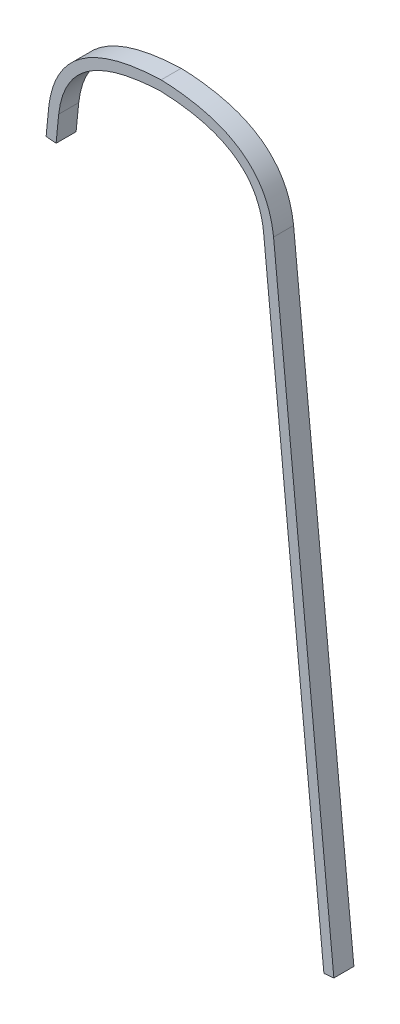
SolidWorks part; units mm, degrees
ref_plane "Front Plane" through (0, 0, 0) normal (0, 0, 1) x (1, 0, 0)
ref_plane "Top Plane" through (0, 0, 0) normal (0, 1, 0) x (1, 0, 0)
ref_plane "Right Plane" through (0, 0, 0) normal (1, 0, 0) x (0, 0, -1)
sketch "Sketch1" plane through (0, 0, 0) normal (0, 0, 1) x (1, 0, 0)
  line L0 (154.7163, 154.5179) -> (97.404, 735.8286)
  line L1 (-99.8892, 710.6217) -> (-97.404, 735.8286)
  line L2 (-109.3682, 711.5562) -> (-99.8892, 710.6217)
  line L3 (154.7163, 154.5179) -> (164.1954, 155.4524)
  line L4 (-166.6875, 130.175) -> (-106.8761, 736.8337) construction
  line L5 (-156.6942, 134.4562) -> (-97.404, 735.8286) construction
  line L6 (-109.3682, 711.5562) -> (-106.8761, 736.8337)
  line L7 (164.1954, 155.4524) -> (106.8761, 736.8337)
  line L8 (0, 0) -> (-166.6875, 130.175) construction
  line L9 (0, 12.0854) -> (-156.6942, 134.4562) construction
  line L10 (0, 0) -> (166.6875, 130.175) construction
  line L11 (0, 12.0854) -> (156.6942, 134.4562) construction
  line L12 (156.6942, 134.4562) -> (97.404, 735.8286) construction
  line L13 (166.6875, 130.175) -> (106.8761, 736.8337) construction
  spline S1 degree 2 poles (-106.8761, 736.8337) (-98.6556, 809.3851) (0, 812.8) knots 0 0 0 1 1 1
  spline S3 degree 2 poles (106.8761, 736.8337) (98.6556, 809.3851) (0, 812.8) knots 0 0 0 1 1 1
  spline S4 degree 1 poles (-97.404, 735.8286) (0, 803.2691) knots 0 0 1 1 construction
  spline S5 degree 1 poles (97.404, 735.8286) (0, 803.2691) knots 0 0 1 1 construction
  spline S8 degree 3 poles (-97.404, 735.8286) (-97.3262, 736.511) (-97.1554, 737.882) (-96.764, 740.5535) (-96.1774, 743.8053) (-95.3214, 747.555) (-93.9799, 752.3593) (-91.9331, 758.0032) (-88.8953, 764.2283) (-85.2743, 769.9432) (-79.6482, 776.9324) (-71.0508, 784.5724) (-60.1295, 790.8325) (-49.8978, 794.9673) (-41.467, 797.6141) (-32.2731, 799.7901) (-23.9758, 801.1984) (-16.9573, 802.076) (-11.5049, 802.6082) (-6.8004, 802.946) (-2.9501, 803.1519) (-0.9798, 803.2339) (0, 803.2691) knots 0.000508 0.000508 0.000508 0.000508 0.016098 0.031688 0.062868 0.094048 0.125228 0.187588 0.249948 0.312308 0.374668 0.499388 0.624108 0.686468 0.748828 0.811188 0.873548 0.904727 0.935907 0.967087 0.982677 0.998267 0.998267 0.998267 0.998267
  spline S9 degree 3 poles (0, 803.2691) (0.9798, 803.2339) (2.9501, 803.1519) (6.8004, 802.946) (11.5049, 802.6082) (16.9573, 802.076) (23.9758, 801.1984) (32.2731, 799.7901) (41.467, 797.6141) (49.8978, 794.9673) (60.1295, 790.8325) (71.0508, 784.5724) (79.6482, 776.9324) (85.2743, 769.9432) (88.8953, 764.2283) (91.9331, 758.0032) (93.9799, 752.3593) (95.3214, 747.555) (96.1774, 743.8053) (96.764, 740.5535) (97.1554, 737.882) (97.3262, 736.511) (97.404, 735.8286) knots 0.000508 0.000508 0.000508 0.000508 0.016098 0.031688 0.062868 0.094048 0.125228 0.187588 0.249948 0.312308 0.374668 0.499388 0.624108 0.686468 0.748828 0.811188 0.873548 0.904727 0.935907 0.967087 0.982677 0.998267 0.998267 0.998267 0.998267
  dimension "D3" = 9.525
  dimension "D4" = 25.4
extrude "Boss-Extrude1" add sketch "Sketch1" along normal blind 19.05
